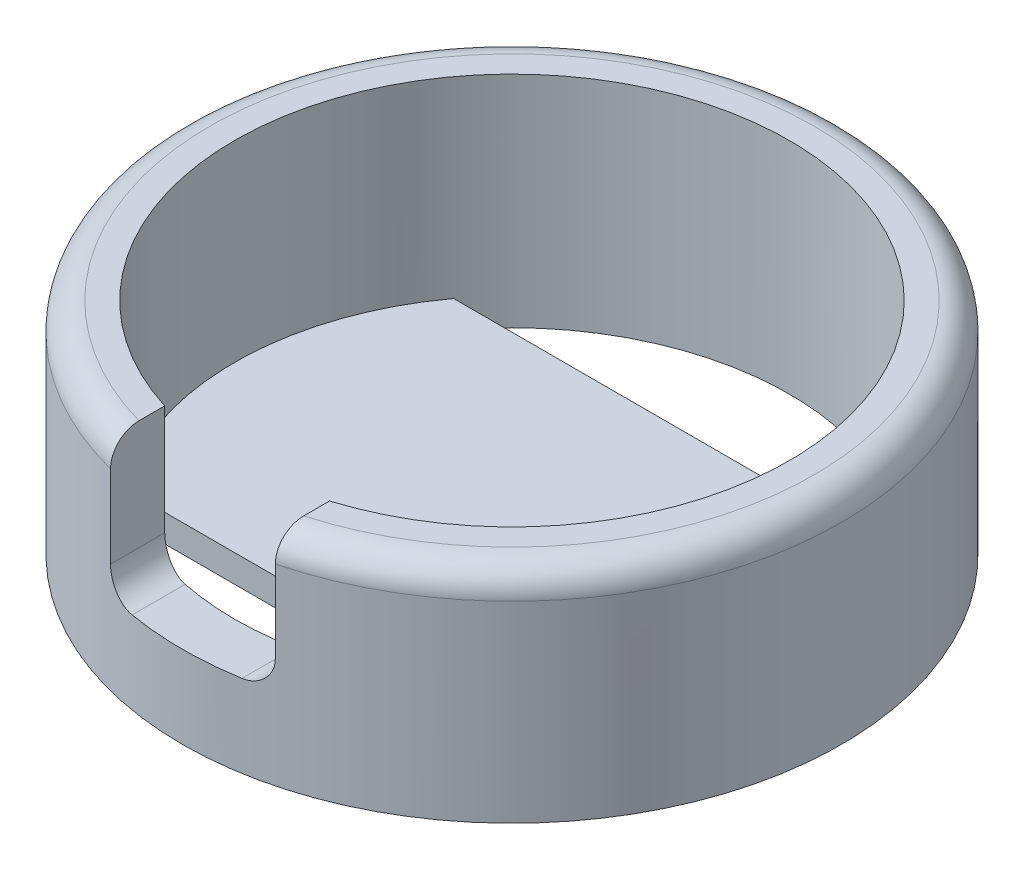
SolidWorks part; units mm, degrees
ref_plane "Front Plane" through (0, 0, 0) normal (0, 0, 1) x (1, 0, 0)
ref_plane "Top Plane" through (0, 0, 0) normal (0, 1, 0) x (1, 0, 0)
ref_plane "Right Plane" through (0, 0, 0) normal (1, 0, 0) x (0, 0, -1)
sketch "Sketch1" plane through (0, 0, 0) normal (0, 1, 0) x (1, 0, 0)
  circle A0 centre (0, 0) radius 6
  circle A1 centre (0, 0) radius 5.05
  dimension "D1" = 12
  dimension "D2" = 10.1
extrude "Boss-Extrude1" add sketch "Sketch1" along normal blind 3.5
sketch "Sketch4" plane through (0, 0, 0) normal (0, -1, 0) x (1, 0, 0)
  circle A0 centre (0, 0) radius 6 construction
  circle A1 centre (0, 0) radius 6
extrude "Boss-Extrude2" add sketch "Sketch4" along normal blind 0.5
sketch "Sketch5" plane through (0, 3.5, 0) normal (0, -1, 0) x (1, 0, 0)
  line L5 (1.5, 6) -> (-1.5, 6)
  line L6 (1.5, 6) -> (1.5, 4.8221)
  line L7 (1.5, 4.8221) -> (-1.5, 4.8221)
  line L8 (-1.5, 6) -> (-1.5, 4.8221)
  circle A3 centre (0, 0) radius 5.05 construction
  circle A4 centre (0, 0) radius 6 construction
  dimension "D1" = 3
extrude "Cut-Extrude3" cut sketch "Sketch5" along normal blind 2.5
sketch "Sketch7" plane through (0, 0, 0) normal (0, 1, 0) x (1, 0, 0)
  line L0 (4.0623, -3) -> (-4.0623, -3)
  line L1 (4.0623, 3) -> (-4.0623, 3)
  circle A0 centre (0, 0) radius 5.05 construction
  circle A1 centre (0, 0) radius 5.05 construction
  arc A2 (4.0623, 3) -> (-4.0623, 3) centre (0, 0) ccw
  arc A3 (-4.0623, -3) -> (4.0623, -3) centre (0, 0) ccw
  dimension "D1" = 6
extrude "Cut-Extrude4" cut sketch "Sketch7" against normal through all
fillet "Fillet1" radius 0.5 3 edges at (0, 3.5, -6) (-1.5, 1, 5.3158) (1.5, 1, 5.3158)
